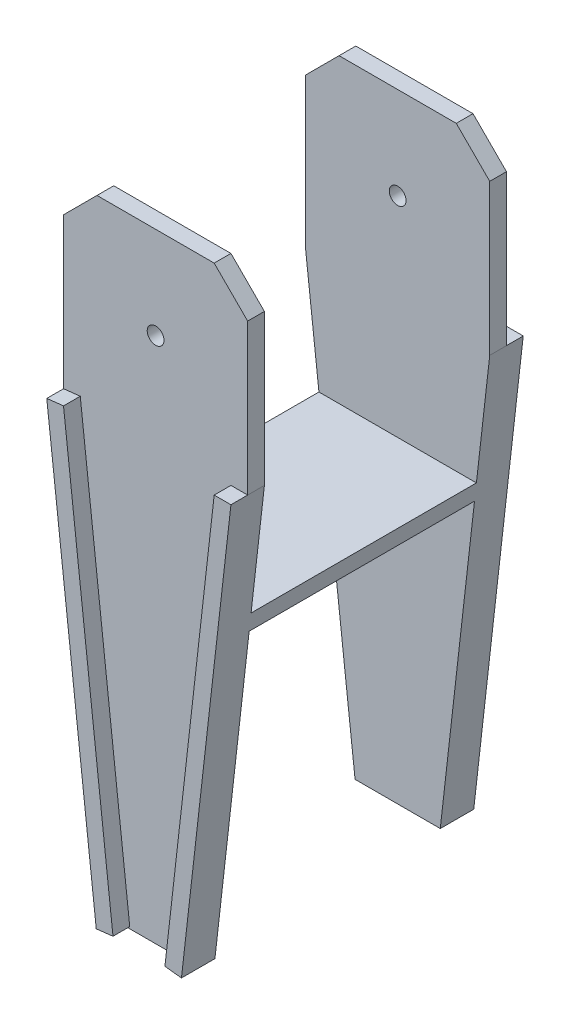
SolidWorks part; units mm, degrees
ref_plane "Ön Düzlem" through (0, 0, 0) normal (0, 0, 1) x (1, 0, 0)
ref_plane "Üst Düzlem" through (0, 0, 0) normal (0, 1, 0) x (1, 0, 0)
ref_plane "Sağ Düzlem" through (0, 0, 0) normal (1, 0, 0) x (0, 0, -1)
sketch "Sketch1" plane through (0, 0, 0) normal (0, 0, 1) x (1, 0, 0)
  line L0 (-27.5, 17.5) -> (-17.5, 27.5)
  line L1 (-17.5, 27.5) -> (17.5, 27.5)
  line L2 (-27.5, 17.5) -> (-27.5, -27.5)
  line L3 (-27.5, -27.5) -> (27.5, -27.5)
  line L4 (27.5, 17.5) -> (27.5, -27.5)
  line L5 (-22.5, 22.5) -> (27.5, -27.5) construction
  line L6 (-27.5, -27.5) -> (22.5, 22.5) construction
  line L7 (17.5, 27.5) -> (27.5, 17.5)
  circle A0 centre (0, 0) radius 2.5
  point P0 (0, 0)
  dimension "D1" = 5
extrude "Boss-Extrude1" add sketch "Sketch1" along normal blind 5
sketch "Sketch3" plane through (0, -27.5, 0) normal (0, -1, 0) x (1, 0, 0)
  line L1 (-27.5, 5) -> (27.5, 5)
  line L2 (-27.5, 5) -> (-27.5, 0)
  line L3 (-27.5, 0) -> (27.5, 0)
  line L4 (27.5, 5) -> (27.5, 0)
extrude "Boss-Extrude2" add sketch "Sketch3" along normal blind 129.8
sketch "Sketch4" plane through (0, 0, 0) normal (0, 0, -1) x (-1, 0, 0)
  line L0 (-27.5, -157.3) -> (-27.5, 17.5) construction
  line L1 (-27.5, -137.3) -> (27.5, -137.3)
  line L2 (-27.5, -137.3) -> (-27.5, -132.3)
  line L3 (-27.5, -132.3) -> (27.5, -132.3)
  line L4 (27.5, -137.3) -> (27.5, -132.3)
  line L5 (27.5, 17.5) -> (27.5, -157.3) construction
  line L6 (27.5, -157.3) -> (-27.5, -157.3) construction
  dimension "D1" = 5
  dimension "D2" = 20
extrude "Boss-Extrude3" add sketch "Sketch4" along normal blind 67.3
sketch "Sketch5" plane through (0, 0, -67.3) normal (0, 0, -1) x (-1, 0, 0)
  line L0 (-27.5, -157.3) -> (27.5, -157.3)
  line L1 (27.5, -157.3) -> (27.5, 17.5)
  line L2 (27.5, 17.5) -> (17.5, 27.5)
  line L3 (17.5, 27.5) -> (-17.5, 27.5)
  line L4 (-17.5, 27.5) -> (-27.5, 17.5)
  line L5 (-27.5, 17.5) -> (-27.5, -157.3)
  circle A0 centre (0, 0) radius 2.5
extrude "Boss-Extrude4" add sketch "Sketch5" along normal blind 5
sketch "Sketch6" plane through (0, 0, 5) normal (0, 0, 1) x (1, 0, 0)
  line L2 (27.5, -157.3) -> (27.5, 17.5) construction
  line L4 (-27.5, 17.5) -> (-27.5, -157.3) construction
  line L6 (-27.5, -27.5) -> (-12.7231, -157.3)
  line L7 (27.5, -157.3) -> (-27.5, -157.3) construction
  line L9 (12.7231, -157.3) -> (27.5, -27.5)
  line L12 (-27.5, -27.5) -> (-27.5, -157.3)
  line L13 (-27.5, -157.3) -> (-12.7231, -157.3)
  line L14 (12.7231, -157.3) -> (27.5, -157.3)
  line L15 (27.5, -157.3) -> (27.5, -27.5)
  line L16 (27.5, -27.5) -> (29.0024, -28.4269)
  line M1 (27.5, -157.3) -> (27.5, 17.5)
  line M5 (-27.5, 17.5) -> (-27.5, -157.3)
  line M6 (-27.5, -157.3) -> (27.5, -157.3)
extrude "Cut-Extrude2" cut sketch "Sketch6" against normal up to next contours L6 M5 M6 | L9 M6 M1
sketch "Sketch7" plane through (0, -137.3, 0) normal (0, -1, 0) x (1, 0, 0)
  line L0 (-15, 0) -> (-15.5692, 0)
  line L2 (-15, 0) -> (-15, -67.3)
  line L4 (15, 0) -> (15, -67.3)
  line L5 (-15.5692, 0) -> (-15.5692, -67.3)
  line L6 (-15.5692, -67.3) -> (-15, -67.3)
  line L7 (15, -67.3) -> (15.5692, -67.3)
  line L8 (15.5692, -67.3) -> (15.5692, 0)
  line L9 (15.5692, 0) -> (15, 0)
extrude "Cut-Extrude3" cut sketch "Sketch7" against normal blind 5
sketch "Sketch8" plane through (0, -137.3, 0) normal (0, -1, 0) x (1, 0, 0)
  line L1 (-15, 0) -> (15, 0)
  line L2 (-15, 0) -> (-15, -67.3)
  line L3 (-15, -67.3) -> (15, -67.3)
  line L4 (15, 0) -> (15, -67.3)
extrude "Cut-Extrude4" cut sketch "Sketch8" against normal up to next
sketch "Sketch9" plane through (0, 0, 0) normal (0, 0, -1) x (-1, 0, 0)
  line L0 (-23.5155, -62.5) -> (23.5155, -62.5)
  line L1 (-12.7231, -157.3) -> (-27.5, -27.5) construction
  line L2 (27.5, -27.5) -> (12.7231, -157.3) construction
  line L3 (23.5155, -62.5) -> (22.9463, -67.5)
  line L4 (22.9463, -67.5) -> (-22.9463, -67.5)
  line L5 (-22.9463, -67.5) -> (-23.5155, -62.5)
  line L6 (-17.5, -27.5) -> (17.5, -27.5) construction
  dimension "D1" = 35
  dimension "D2" = 5
extrude "Boss-Extrude5" add sketch "Sketch9" along normal up to next
sketch "Sketch10" plane through (0, 0, 5) normal (0, 0, 1) x (1, 0, 0)
  line L0 (27.5, -27.5) -> (12.7231, -157.3)
  line L1 (12.7231, -157.3) -> (7.7871, -156.7381)
  line L2 (7.7871, -156.7381) -> (22.5, -27.5)
  line L3 (22.5, -27.5) -> (27.5, -27.5)
  line L4 (-27.5, -27.5) -> (-12.7231, -157.3)
  line L5 (-12.7231, -157.3) -> (-7.7231, -156.7308)
  line L6 (-7.7231, -156.7308) -> (-22.5, -26.9308)
  line L7 (-22.5, -26.9308) -> (-27.5, -27.5)
  dimension "D1" = 5
  dimension "D2" = 5
extrude "Boss-Extrude6" add sketch "Sketch10" along normal blind 5
sketch "Sketch11" plane through (0, 0, -72.3) normal (0, 0, -1) x (-1, 0, 0)
  line L0 (-27.5, -27.5) -> (-12.7231, -157.3)
  line L1 (-12.7231, -157.3) -> (-7.7871, -156.7381)
  line L2 (-7.7871, -156.7381) -> (-22.5, -27.5)
  line L3 (-22.5, -27.5) -> (-27.5, -27.5)
  line L4 (27.5, -27.5) -> (12.7231, -157.3)
  line L5 (12.7231, -157.3) -> (7.7552, -156.7344)
  line L6 (7.7552, -156.7344) -> (22.5321, -26.9344)
  line L7 (22.5321, -26.9344) -> (27.5, -27.5)
  dimension "D1" = 5
  dimension "D2" = 5
extrude "Boss-Extrude7" add sketch "Sketch11" along normal blind 5
